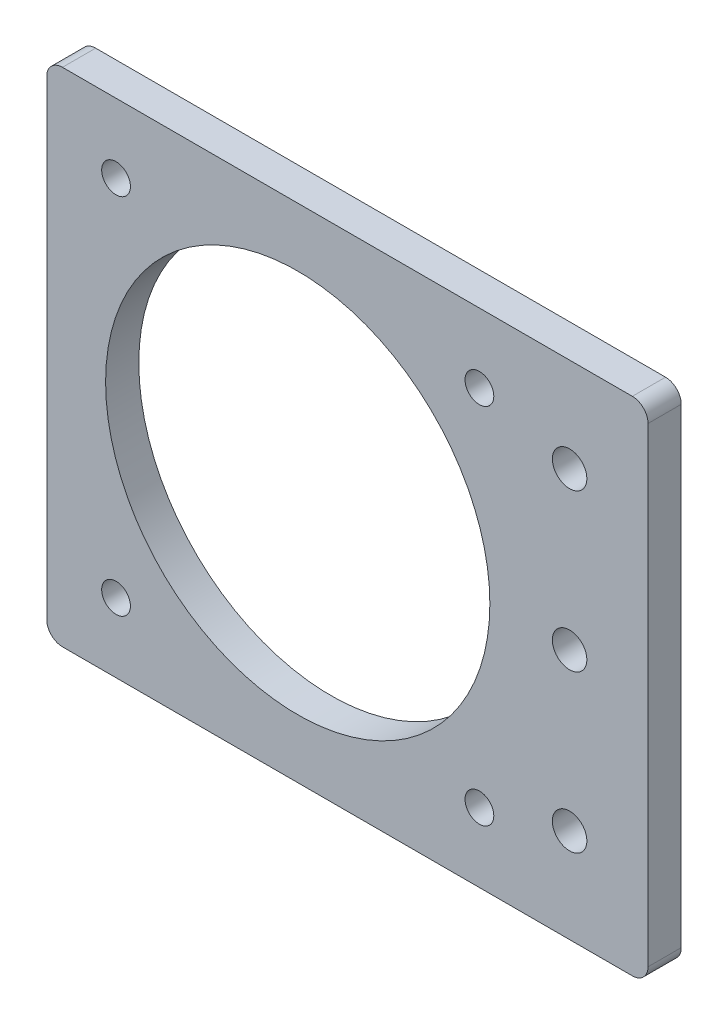
SolidWorks part; units mm, degrees
ref_plane "Front" through (0, 0, 0) normal (0, 0, 1) x (1, 0, 0)
ref_plane "Top" through (0, 0, 0) normal (0, 1, 0) x (1, 0, 0)
ref_plane "Right" through (0, 0, 0) normal (1, 0, 0) x (0, 0, -1)
sketch "Sketch1" plane through (0, 0, 0) normal (0, 0, 1) x (1, 0, 0)
  line L1 (-57.5, -48) -> (57.5, -48)
  line L2 (-57.5, -48) -> (-57.5, 48)
  line L3 (-57.5, 48) -> (57.5, 48)
  line L4 (57.5, -48) -> (57.5, 48)
  line L5 (0, 48) -> (0, -48) construction
  line L6 (-57.5, 0) -> (57.5, 0) construction
  point P0 (0, 0)
  dimension "D1" = 96
  dimension "D2" = 115
extrude "Boss-Extrude1" add sketch "Sketch1" along normal blind 6.35
sketch "Sketch2" plane through (0, 0, 6.35) normal (0, 0, 1) x (1, 0, 0)
  line L0 (-57.5, 48) -> (-9.5, 0) construction
  line L1 (-9.5, 0) -> (-57.5, -48) construction
  circle A0 centre (-9.5, 0) radius 36.75
  dimension "D1" = 73.5
extrude "Cut-Extrude1" cut sketch "Sketch2" against normal through all
fillet "Fillet1" radius 3 4 edges at (57.5, -48, 3.175) (-57.5, -48, 3.175) (57.5, 48, 3.175) (-57.5, 48, 3.175)
hole_wizard "M6 Clearance Hole1" positions "Sketch5" profile "Sketch4" hole size "M6" standard "ANSI Metric"
sketch "Sketch5" plane through (0, 0, 6.35) normal (0, 0, 1) x (1, 0, 0)
  line L0 (57.5, -45) -> (57.5, 45) construction
  point P0 (42.5, 30)
  point P2 (42.5, 0)
  point P4 (42.5, -30)
  dimension "D1" = 15
  dimension "D2" = 30
  dimension "D3" = 30
sketch "Sketch4" plane through (42.5, 30, 6.35) normal (1, 0, 0) x (0, -1, 0)
  line L0 (0, 0) -> (0, 21.9828)
  line L1 (0, 21.9828) -> (3.3, 20)
  line L2 (3.3, 20) -> (3.3, 0)
  line L5 (3.3, 0) -> (0, 0)
  line L10 (0, 21.9828) -> (-3.3, 20) construction
  line L11 (0, -6.35) -> (0, 107.95) construction
  dimension "Hole Dia." = 6.6
  dimension "Hole Depth" = 20
  dimension "Drill Angle" = 118
hole_wizard "M5 Clearance Hole1" positions "Sketch7" profile "Sketch6" hole size "M5" standard "ANSI Metric" end condition through all
sketch "Sketch7" plane through (0, 0, 6.35) normal (0, 0, 1) x (1, 0, 0)
  line L1 (-44.25, 34.75) -> (25.25, 34.75) construction
  line L2 (25.25, 34.75) -> (25.25, -34.75) construction
  line L3 (25.25, -34.75) -> (-44.25, -34.75) construction
  line L4 (-44.25, -34.75) -> (-44.25, 34.75) construction
  line L9 (-9.5, 0) -> (-9.5, 34.75) construction
  line L12 (-44.25, 0) -> (-9.5, 0) construction
  point P0 (25.25, -34.75)
  point P2 (-44.25, -34.75)
  point P4 (-44.25, 34.75)
  point P6 (25.25, 34.75)
  dimension "D1" = 69.5
  dimension "D2" = 69.5
sketch "Sketch6" plane through (25.25, -34.75, 6.35) normal (1, 0, 0) x (0, -1, 0)
  line L0 (0, 0) -> (0, 6.35)
  line L1 (0, 6.35) -> (2.75, 6.35)
  line L2 (2.75, 6.35) -> (2.75, 0)
  line L5 (2.75, 0) -> (0, 0)
  line L11 (0, -6.35) -> (0, 107.95) construction
  dimension "Thru Hole Dia." = 5.5
  dimension "Thru Hole Depth" = 6.35
